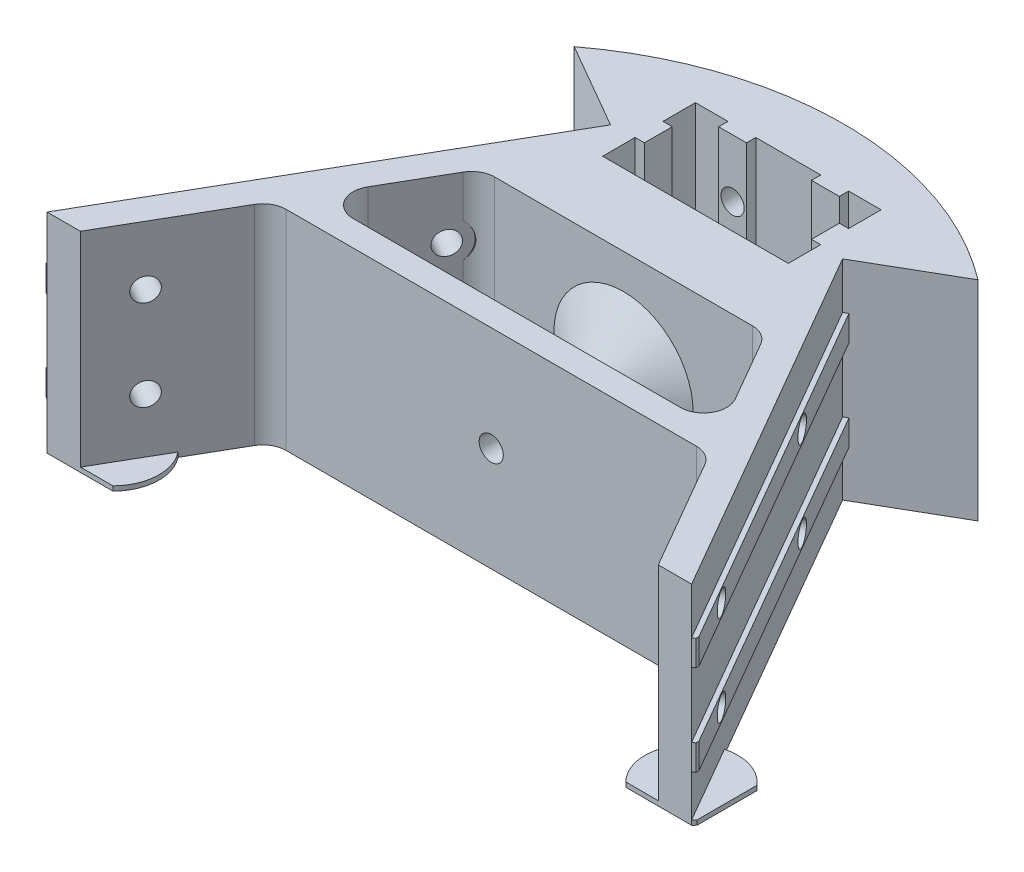
SolidWorks part; units mm, degrees
material "ABS"
ref_plane "Front Plane" through (0, 0, 0) normal (0, 0, 1) x (1, 0, 0)
ref_plane "Top Plane" through (0, 0, 0) normal (0, 1, 0) x (1, 0, 0)
ref_plane "Right Plane" through (0, 0, 0) normal (1, 0, 0) x (0, 0, -1)
sketch "Sketch1" plane through (0, 0, 0) normal (0, 1, 0) x (1, 0, 0)
  line L0 (0, -40) -> (0, 0) construction
  line L1 (-20, 20) -> (-13, 20)
  line L2 (-13, 20) -> (-13, 18)
  line L3 (-13, 18) -> (-7, 18)
  line L4 (-7, 18) -> (-7, 20)
  line L5 (-7, 20) -> (7, 20)
  line L6 (7, 20) -> (7, 18)
  line L7 (7, 18) -> (13, 18)
  line L8 (13, 18) -> (13, 20)
  line L9 (13, 20) -> (20, 20)
  line L10 (20, 20) -> (20, 13)
  line L11 (20, 13) -> (18, 13)
  line L12 (18, 13) -> (18, 7)
  line L13 (18, 7) -> (20, 7)
  line L14 (20, 7) -> (20, 0)
  line L15 (0, 20) -> (0, 0) construction
  line L16 (0, 0) -> (0, 50) construction
  line L17 (0, 50) -> (7.5492, 36.9243) construction
  line L18 (34.641, 70) -> (134.641, -103.2051) construction
  line L19 (20, 0) -> (-20, 0)
  line L20 (0, 50) -> (34.641, 70) construction
  line L21 (134.641, -103.2051) -> (100, -123.2051) construction
  line L22 (67.0736, -66.1749) -> (25, 6.6987)
  line L23 (25, 6.6987) -> (43.4956, 17.3771)
  line L24 (-20, 0) -> (-20, 7)
  line L25 (-20, 7) -> (-18, 7)
  line L26 (-18, 7) -> (-18, 13)
  line L27 (-18, 13) -> (-20, 13)
  line L28 (-20, 13) -> (-20, 20)
  line L29 (59.641, 26.6987) -> (134.641, -103.2051) construction
  line L30 (0, 50) -> (-7.0324, 37.8196) construction
  line L31 (0, 50) -> (-34.641, 70) construction
  line L32 (-34.641, 70) -> (-134.641, -103.2051) construction
  line L33 (-134.641, -103.2051) -> (-59.641, 26.6987) construction
  line L34 (-43.4956, 17.3771) -> (-25, 6.6987)
  line L35 (-25, 6.6987) -> (-67.0736, -66.1749)
  line L36 (-100, -123.2051) -> (-134.641, -103.2051) construction
  line L37 (0, -40) -> (0, -15.5) construction
  line L38 (-27.7444, -15.5) -> (27.7444, -15.5)
  line L39 (-35.25, -38.5) -> (35.25, -38.5)
  line L40 (-32.0746, -18) -> (-39.5801, -31)
  line L41 (32.0746, -18) -> (39.5801, -31)
  line L42 (-39.5801, -31) -> (-44.9691, -27.8887) construction
  line L43 (-39.5801, -31) -> (-47.1202, -44.0598) construction
  line L44 (-32.0746, -18) -> (-43.2264, -37.3156) construction
  line L45 (-37.4635, -14.8887) -> (-32.0746, -18) construction
  line L46 (-48.5291, -46.5) -> (-63.915, -73.1492)
  line L47 (-44.1989, -44) -> (44.1989, -44)
  line L48 (32.0746, -18) -> (39.5801, -31) construction
  line L49 (39.5801, -31) -> (48.7394, -46.8643) construction
  line L50 (48.5291, -46.5) -> (63.915, -73.1492)
  line L51 (-67.0736, -66.1749) -> (-71.1002, -73.1492)
  line L52 (-71.1002, -73.1492) -> (-63.915, -73.1492)
  line L53 (67.0736, -66.1749) -> (71.1002, -73.1492)
  line L54 (71.1002, -73.1492) -> (63.915, -73.1492)
  arc A0 (63.915, -73.1492) -> (67.0736, -66.1749) centre (0, -40) ccw construction
  arc A1 (-27.7444, -15.5) -> (-32.0746, -18) centre (-27.7444, -20.5) ccw
  arc A2 (32.0746, -18) -> (27.7444, -15.5) centre (27.7444, -20.5) ccw
  arc A3 (35.25, -38.5) -> (39.5801, -31) centre (35.25, -33.5) ccw
  arc A4 (-39.5801, -31) -> (-35.25, -38.5) centre (-35.25, -33.5) ccw
  arc A5 (-44.1989, -44) -> (-48.5291, -46.5) centre (-44.1989, -49) ccw
  arc A6 (48.5291, -46.5) -> (44.1989, -44) centre (44.1989, -49) ccw
  arc A7 (-67.0736, -66.1749) -> (-63.915, -73.1492) centre (0, -40) ccw construction
  arc A8 (43.4956, 17.3771) -> (-43.4956, 17.3771) centre (0, -40) ccw
  dimension "D1" = 144
  dimension "D14" = 10
  dimension "D2" = 40
  dimension "D3" = 6
  dimension "D4" = 2
  dimension "D5" = 40
  dimension "D6" = 20
  dimension "D7" = 50
  dimension "D8" = 30
  dimension "D9" = 40
  dimension "D10" = 200
  dimension "D11" = 150
  dimension "D12" = 30
  dimension "D13" = 1.5
  dimension "D15" = 13
  dimension "D17" = 70.5
  dimension "D18" = 5.5
extrude "Boss-Extrude1" add sketch "Sketch1" along normal blind 45
sketch "Sketch3" plane through (21.6506, 0, -12.5) normal (0.866, 0, -0.5) x (-0.5, 0, -0.866)
  line L0 (-98.8992, 35) -> (-6.6987, 35)
  line L1 (-98.8992, 45) -> (-98.8992, 0) construction
  line L2 (-6.6987, 45) -> (-6.6987, 0) construction
  line L3 (-6.6987, 35) -> (-6.6987, 29.5)
  line L4 (-6.6987, 29.5) -> (-98.8992, 29.5)
  line L5 (-98.8992, 29.5) -> (-98.8992, 35)
  line L6 (-98.8992, 15.5) -> (-6.6987, 15.5)
  line L7 (-6.6987, 15.5) -> (-6.6987, 10)
  line L8 (-6.6987, 10) -> (-98.8992, 10)
  line L9 (-98.8992, 10) -> (-98.8992, 15.5)
  line L10 (-98.8992, 22.5) -> (-6.6987, 22.5) construction
  line L11 (-6.6987, 45) -> (-6.6987, 0) construction
  line L12 (-98.8992, 22.5) -> (-98.8992, 29.5) construction
  line L13 (-98.8992, 22.5) -> (-98.8992, 15.5) construction
  dimension "D1" = 5.5
  dimension "D2" = 7
extrude "Boss-Extrude2" add sketch "Sketch3" along normal blind 1
sketch "Sketch4" plane through (22.5167, 0, -13) normal (0.866, 0, -0.5) x (-0.5, 0, -0.866)
  line L0 (-6.6987, 32.25) -> (-98.8992, 32.25) construction
  line L1 (-6.6987, 29.5) -> (-6.6987, 35) construction
  line L2 (-98.8992, 35) -> (-98.8992, 29.5) construction
  line L3 (-98.8992, 12.75) -> (-6.6987, 12.75) construction
  line L4 (-98.8992, 15.5) -> (-98.8992, 10) construction
  line L5 (-6.6987, 10) -> (-6.6987, 15.5) construction
  line L6 (-6.6987, 45) -> (-6.6987, 0) construction
  circle A0 centre (-34.1987, 32.25) radius 2.5
  circle A1 centre (-34.1987, 12.75) radius 2.5
  circle A2 centre (-81.6987, 12.75) radius 2.5
  circle A3 centre (-81.6987, 32.25) radius 2.5
  dimension "D1" = 5
  dimension "D3" = 75
  dimension "D2" = 27.5
extrude "Cut-Extrude2" cut sketch "Sketch4" against normal up to next (7.2226 mm away)
sketch "Sketch8" plane through (16.2617, 0, -9.3887) normal (-0.866, 0, 0.5) x (0.5, 0, 0.866)
  circle A0 centre (34.1987, 32.25) radius 4.5
  circle A1 centre (34.1987, 12.75) radius 4.5
  dimension "D1" = 9
extrude "Cut-Extrude7" cut sketch "Sketch8" along normal up to next
sketch "Sketch5" plane through (0, 0, -18) normal (0, 0, 1) x (1, 0, 0)
  line L0 (7, 22.5) -> (13, 22.5) construction
  line L1 (7, 45) -> (7, 0) construction
  line L2 (13, 45) -> (13, 0) construction
  line L3 (10, 22.5) -> (10, 32.5) construction
  line L4 (10, 22.5) -> (10, 12.5) construction
  circle A0 centre (10, 32.5) radius 2.5
  circle A1 centre (10, 12.5) radius 2.5
  dimension "D1" = 20
  dimension "D2" = 5
extrude "Cut-Extrude3" cut sketch "Sketch5" against normal up to next
sketch "Sketch6" plane through (0, 0, -18) normal (0, 0, 1) x (1, 0, 0)
  circle A0 centre (10, 32.5) radius 4.25
  circle A1 centre (10, 12.5) radius 4.25
  dimension "D1" = 8.5
extrude "Cut-Extrude5" cut sketch "Sketch6" along normal blind 1.7 from offset 14 offset against normal yes
mirror "Mirror1" about plane through (0, 0, 0) normal (1, 0, 0) of "Cut-Extrude7", "Cut-Extrude5", "Cut-Extrude3", "Cut-Extrude2", "Boss-Extrude2"
sketch "Sketch7" plane through (0, 45, 0) normal (0, 1, 0) x (1, 0, 0)
  line L0 (-2.6, -5.6) -> (-2.6, -8.4)
  line L1 (2.6, -5.6) -> (2.6, -8.4)
  line L4 (-20, 0) -> (20, 0) construction
  line L5 (0, 0) -> (0, -5.6) construction
  arc A0 (2.6, -5.6) -> (-2.6, -5.6) centre (0, -5.6) ccw
  arc A1 (-2.6, -8.4) -> (2.6, -8.4) centre (0, -8.4) ccw
  dimension "D1" = 5.2
  dimension "D2" = 2.8
  dimension "D3" = 5.6
extrude "Cut-Extrude6" [suppressed] cut sketch "Sketch7" against normal up to next
sketch "Sketch9" plane through (0, 0, 0) normal (1, 0, 0) x (0, 0, -1)
  line L0 (-15.5, 22.5) -> (-38.5, 22.5) construction
  line L1 (-15.5, 45) -> (-15.5, 0) construction
  line L2 (-31.1, 26.1) -> (-31.1, 22.5)
  line L3 (-22.9, 26.1) -> (-15.5, 37.5)
  line L4 (0, 45) -> (0, 0) construction
  line L5 (-38.5, 37.5) -> (-31.1, 26.1)
  line L6 (-38.5, 45) -> (-38.5, 0) construction
  line L7 (-31.1, 22.5) -> (-38.5, 22.5)
  line L8 (-38.5, 22.5) -> (-38.5, 37.5)
  line L9 (-22.9, 26.1) -> (-22.9, 22.5)
  line L10 (-22.9, 22.5) -> (-15.5, 22.5)
  line L11 (-15.5, 22.5) -> (-15.5, 37.5)
  dimension "D1" = 8.2
  dimension "D2" = 15
  dimension "D3" = 3.6
  dimension "D4" = 22.9
revolve "Revolve1" add sketch "Sketch9" angle 360 about L0
sketch "Sketch10" plane through (0, 0, 44) normal (0, 0, 1) x (1, 0, 0)
  line L0 (0, 45) -> (0, 0) construction
  line L1 (-44.1989, 45) -> (44.1989, 45) construction
  circle A0 centre (0, 22.5) radius 2.6
  dimension "D1" = 5.2
extrude "Cut-Extrude8" cut sketch "Sketch10" against normal blind 32
sketch "Sketch11" plane through (0, 0, 0) normal (0, 1, 0) x (1, 0, 0)
  line L0 (59.2113, -65.0022) -> (65.4663, -61.3909) construction
  line L1 (48.5291, -46.5) -> (63.915, -73.1492) construction
  line L2 (25.866, 7.1987) -> (71.9663, -72.6492) construction
  line L3 (-59.2113, -65.0022) -> (-65.4663, -61.3909) construction
  line L4 (-63.915, -73.1492) -> (-48.5291, -46.5) construction
  line L5 (-25.866, 7.1987) -> (-71.9663, -72.6492) construction
  line L6 (71.9663, -72.6492) -> (71.1002, -73.1492) construction
  circle A0 centre (62.3388, -63.1966) radius 10
  circle A1 centre (-62.3388, -63.1966) radius 10
  dimension "D2" = 20
  dimension "D1" = 13
extrude "Boss-Extrude3" add sketch "Sketch11" along normal blind 1
sketch "Sketch12" plane through (49.4496, 0, 85.6492) normal (0.5, 0, 0.866) x (0.866, 0, -0.5)
  line L0 (25, 29.5) -> (26, 29.5)
  line L1 (26, 29.5) -> (25, 27.3555)
  line L2 (25, 29.5) -> (25, 15.5) construction
  line L3 (25, 27.3555) -> (25, 29.5)
  line L4 (25, 10) -> (26, 10)
  line L5 (26, 10) -> (25, 7.8555)
  line L6 (25, 10) -> (25, 0) construction
  line L7 (25, 7.8555) -> (25, 10)
  dimension "D1" = 65
extrude "Boss-Extrude4" [suppressed] add sketch "Sketch12" against normal blind 0.7
pattern_linear "LPattern1" [suppressed] count 46 spacing 2
sketch "Sketch13" plane through (-49.4496, 0, 85.6492) normal (-0.5, 0, 0.866) x (0.866, 0, 0.5)
  line L0 (-25, 29.5) -> (-26, 29.5)
  line L1 (-26, 29.5) -> (-25, 27.3555)
  line L2 (-25, 29.5) -> (-25, 15.5) construction
  line L3 (-25, 27.3555) -> (-25, 29.5)
  line L4 (-25, 10) -> (-26, 10)
  line L5 (-26, 10) -> (-25, 7.8555)
  line L6 (-25, 10) -> (-25, 0) construction
  line L7 (-25, 7.8555) -> (-25, 10)
  dimension "D1" = 65
extrude "Boss-Extrude5" [suppressed] add sketch "Sketch13" against normal blind 0.7
pattern_linear "LPattern2" [suppressed] count 46 spacing 2
sketch "Sketch14" plane through (0, 0, 0) normal (0, 1, 0) x (1, 0, 0)
  line L0 (-80, -75.1492) -> (80, -75.1492)
  line L1 (80, -75.1492) -> (80, -53.1492)
  line L2 (80, -53.1492) -> (70, -53.1492)
  line L3 (70, -53.1492) -> (70, -69.9178)
  line L4 (-71.1002, -73.1492) -> (-63.915, -73.1492) construction
  line L5 (70, -69.9178) -> (69.4259, -70.2492)
  line L7 (71.1002, -73.1492) -> (25, 6.6987) construction
  line L8 (69.4259, -70.2492) -> (-69.4259, -70.2492)
  line L9 (-25, 6.6987) -> (-71.1002, -73.1492) construction
  line L10 (-69.4259, -70.2492) -> (-70, -69.9178)
  line L12 (-70, -69.9178) -> (-70, -53.1492)
  line L13 (-70, -53.1492) -> (-80, -53.1492)
  line L14 (-80, -53.1492) -> (-80, -75.1492)
  line L15 (25, 6.6987) -> (71.1002, -73.1492) construction
  dimension "D1" = 80
  dimension "D2" = 160
  dimension "D3" = 10
  dimension "D4" = 22
  dimension "D5" = 4.9
  dimension "D6" = 2
extrude "Cut-Extrude10" cut sketch "Sketch14" along normal through all
equation "\"D12@Sketch1\"=\"D8@Sketch1\""
equation "\"D2@Sketch3\"=(20-6)/2"
equation "\"D4@Sketch9\"=27-\"D1@Sketch9\"/2"
